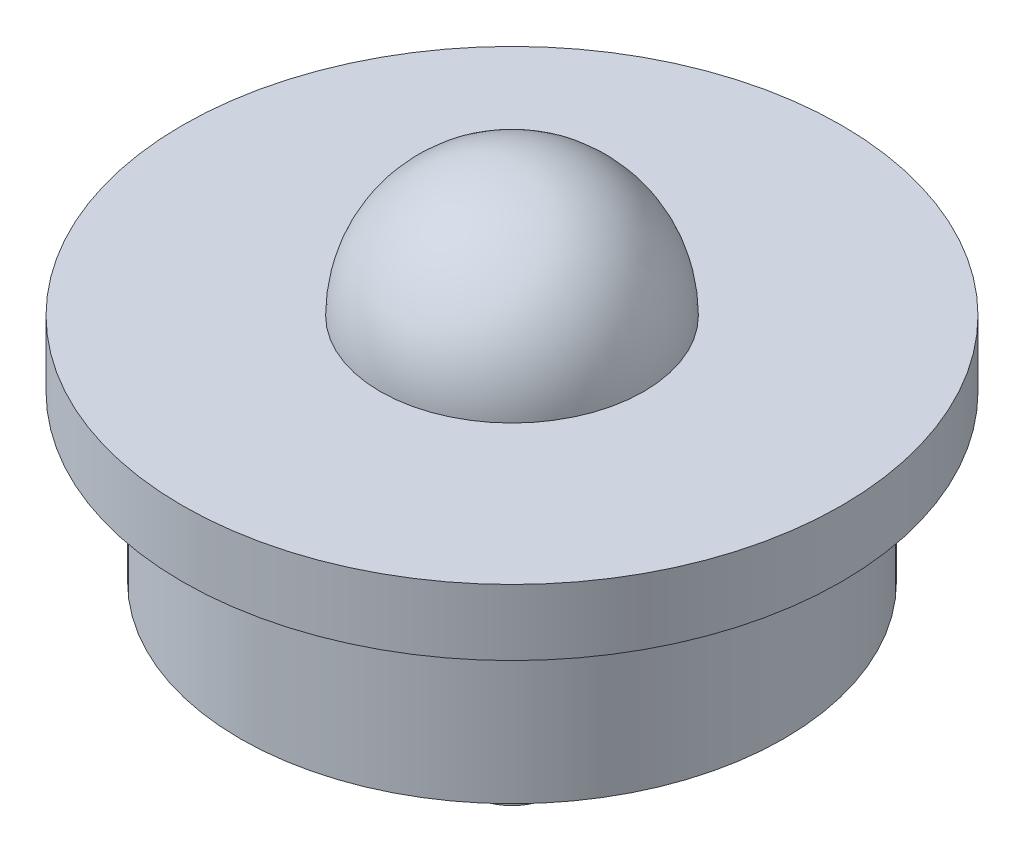
SolidWorks part; units mm, degrees
ref_plane "Front Plane" through (0, 0, 0) normal (0, 0, 1) x (1, 0, 0)
ref_plane "Top Plane" through (0, 0, 0) normal (0, 1, 0) x (1, 0, 0)
ref_plane "Right Plane" through (0, 0, 0) normal (1, 0, 0) x (0, 0, -1)
sketch "Sketch1" plane through (0, 0, 0) normal (0, 1, 0) x (1, 0, 0)
  circle A0 centre (0, 0) radius 26.1937
  dimension "D1" = 52.3875
extrude "Boss-Extrude1" add sketch "Sketch1" along normal blind 22.225
sketch "Sketch2" plane through (0, 22.225, 0) normal (0, 1, 0) x (1, 0, 0)
  circle A0 centre (0, 0) radius 31.75
  dimension "D1" = 63.5
extrude "Boss-Extrude2" add sketch "Sketch2" against normal blind 6.35
sketch "Sketch3" plane through (0, 22.225, 0) normal (0, 1, 0) x (1, 0, 0)
  line L0 (0, 45.3791) -> (0, -38.0659) construction
  line L1 (0, -12.7) -> (0, 12.7)
  arc A0 (0, -12.7) -> (0, 12.7) centre (0, 0) ccw
  dimension "D1" = 25.4
revolve "Revolve1" add sketch "Sketch3" angle 360 about L0
sketch "Sketch4" plane through (0, 0, 0) normal (0, -1, 0) x (1, 0, 0)
  circle A0 centre (0, 0) radius 3.9688
  dimension "D1" = 7.9375
extrude "Boss-Extrude3" add sketch "Sketch4" along normal blind 15.875
